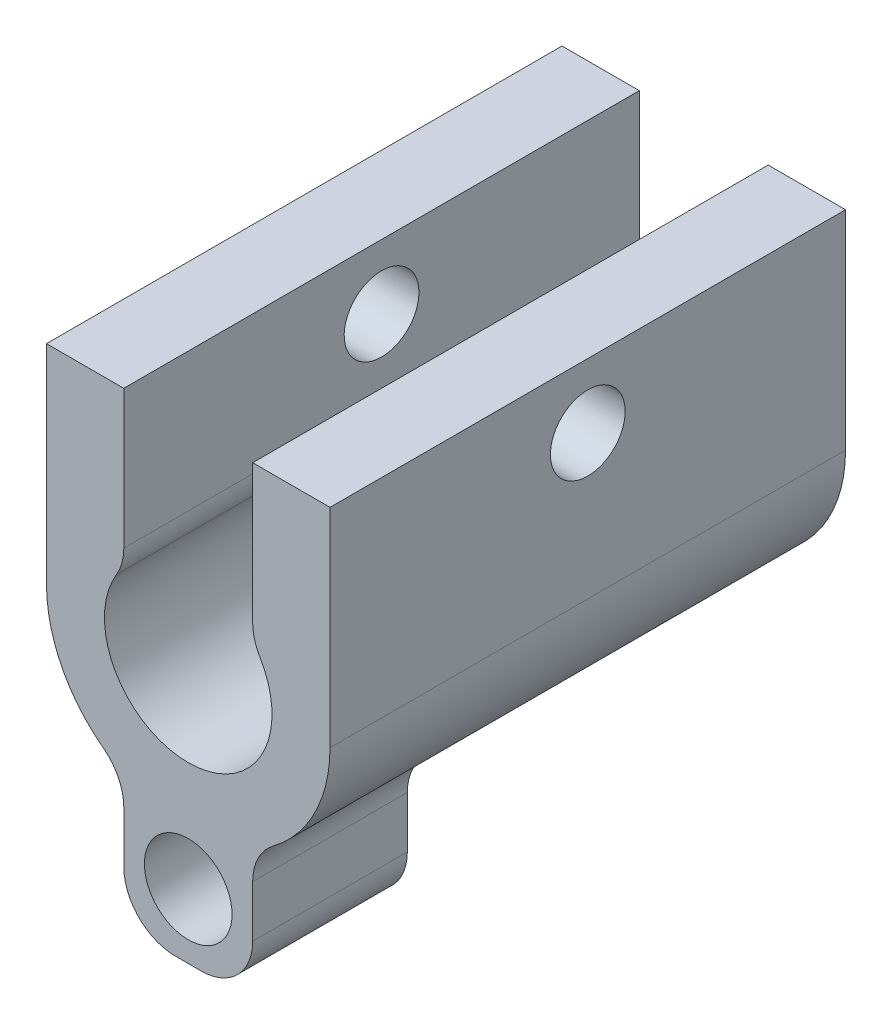
SolidWorks part; units mm, degrees
material "PMMA"
ref_plane "Plan de face" through (0, 0, 0) normal (0, 0, 1) x (1, 0, 0)
ref_plane "Plan de dessus" through (0, 0, 0) normal (0, 1, 0) x (1, 0, 0)
ref_plane "Plan de droite" through (0, 0, 0) normal (1, 0, 0) x (0, 0, -1)
sketch "Esquisse1" plane through (0, 0, 0) normal (0, 0, 1) x (1, 0, 0)
  line L0 (-5.5, 0) -> (-5.5, 8.0767)
  line L1 (-5.5, 8.0767) -> (-2.5, 8.0767)
  line L3 (-2.5, 8.0767) -> (-2.5, 2.0767)
  line L4 (5.5, 0) -> (5.5, 8.0767)
  line L5 (5.5, 8.0767) -> (2.5, 8.0767)
  line L6 (2.5, 8.0767) -> (2.5, 2.0767)
  line L7 (0, 0) -> (0, 8.0767) construction
  line L8 (-2.5, -6) -> (-2.5, -8)
  line L9 (-0.5, -10) -> (0.5, -10)
  line L10 (2.5, -8) -> (2.5, -6)
  arc A0 (-2.5, 2.0767) -> (2.5, 2.0767) centre (0, 0) ccw
  arc A1 (-5.5, 0) -> (-3.3, -4.4) centre (0, 0) ccw
  arc A2 (3.3, -4.4) -> (5.5, 0) centre (0, 0) ccw
  arc A5 (-0.5, -10) -> (-2.5, -8) centre (-0.5, -8) cw
  arc A6 (0.5, -10) -> (2.5, -8) centre (0.5, -8) ccw
  arc A7 (3.3, -4.4) -> (2.5, -6) centre (4.5, -6) ccw
  arc A8 (-3.3, -4.4) -> (-2.5, -6) centre (-4.5, -6) cw
  point P9 (-3.5126, 6)
  point P11 (-3.3, 2.2646)
  point P14 (2.8796, 1.7884)
  point P16 (0, 7.3748)
  point P19 (-2.5, 2.0767)
  point P22 (-2.5, -10)
  point P25 (2.5, -10)
  point P28 (2.5, -4.899)
  point P31 (-1.8147, 3.3173)
  point P32 (-2.8097, 1.6866)
  point P33 (0, 0)
  dimension "D1" = 3.25
  dimension "D2" = 5.5
  dimension "D6" = 3
  dimension "D7" = 2
  dimension "D3" = 6
  dimension "D4" = 10
  dimension "D5" = 5
extrude "Boss.-Extru.1" add sketch "Esquisse1" along normal blind 20
hole_wizard "Dégagement M2.51" positions "Esquisse2" profile "Esquisse3" hole size "M2.5" standard "DIN" end condition through all
sketch "Esquisse2" plane through (5.5, 0, 0) normal (1, 0, 0) x (0, 0, -1)
  line L0 (-10, 5.5767) -> (0, 5.5767) construction
  line L3 (-10, 5.5767) -> (-10, 8.0767) construction
  line L4 (-20, 8.0767) -> (0, 8.0767) construction
  point P0 (-10, 5.5767)
  dimension "D1" = 2.5
sketch "Esquisse3" plane through (5.5, 5.5767, 10) normal (0, 1, 0) x (0, 0, -1)
  line L0 (0, 0) -> (0, 11)
  line L1 (0, 11) -> (1.45, 11)
  line L2 (1.45, 11) -> (1.45, 0)
  line L5 (1.45, 0) -> (0, 0)
  line L11 (0, -6.35) -> (0, 107.95) construction
  dimension "Diamètre du perçage jusqu'au prochain" = 2.9
  dimension "Profondeur du perçage jusqu'au prochain" = 11
sketch "Esquisse5" plane through (0, 0, 0) normal (0, 0, -1) x (-1, 0, 0)
  line L0 (-2.5, -6) -> (-2.5, -8)
  line L1 (-0.5, -10) -> (0.5, -10)
  line L2 (2.5, -8) -> (2.5, -6)
  line L3 (-3.3, -4.4) -> (3.3, -4.4)
  arc A0 (-2.5, -6) -> (-3.3, -4.4) centre (-4.5, -6) ccw
  arc A1 (3.3, -4.4) -> (2.5, -6) centre (4.5, -6) ccw
  arc A2 (-2.5, -8) -> (-0.5, -10) centre (-0.5, -8) ccw
  arc A3 (0.5, -10) -> (2.5, -8) centre (0.5, -8) ccw
extrude "Enlèv. mat.-Extru.1" cut sketch "Esquisse5" against normal offset from surface (14 mm away) 6 up to face at (0, -1.6766, 20)
hole_wizard "Dégagement M31" positions "Esquisse3D1" profile "Esquisse4" hole size "M3" standard "DIN" end condition through all
sketch3d "Esquisse3D1"
  line L0 (0, -7.5, 20) -> (0, -3.25, 20) construction
  line L2 (0, -7.5, 20) -> (0, -10, 20) construction
  line L3 (-0.5, -10, 20) -> (0.5, -10, 20) construction
  arc A0 (2.5, 2.0767, 20) -> (-2.5, 2.0767, 20) centre (0, 0, 20) ccw construction
  point P0 (0, -7.5, 20)
  point P8 (0, 0, 16.75)
  dimension "D1" = 2.5
sketch "Esquisse4" plane through (0, -7.5, 20) normal (1, 0, 0) x (0, -1, 0)
  line L0 (0, 0) -> (0, 20)
  line L1 (0, 20) -> (1.7, 20)
  line L2 (1.7, 20) -> (1.7, 0)
  line L5 (1.7, 0) -> (0, 0)
  line L11 (0, -6.35) -> (0, 107.95) construction
  dimension "Diamètre du perçage jusqu'au prochain" = 3.4
  dimension "Profondeur du perçage jusqu'au prochain" = 20
fillet "Congé1" radius 2 2 edges at (2.5, 2.0767, 10) (-2.5, 2.0767, 10)
